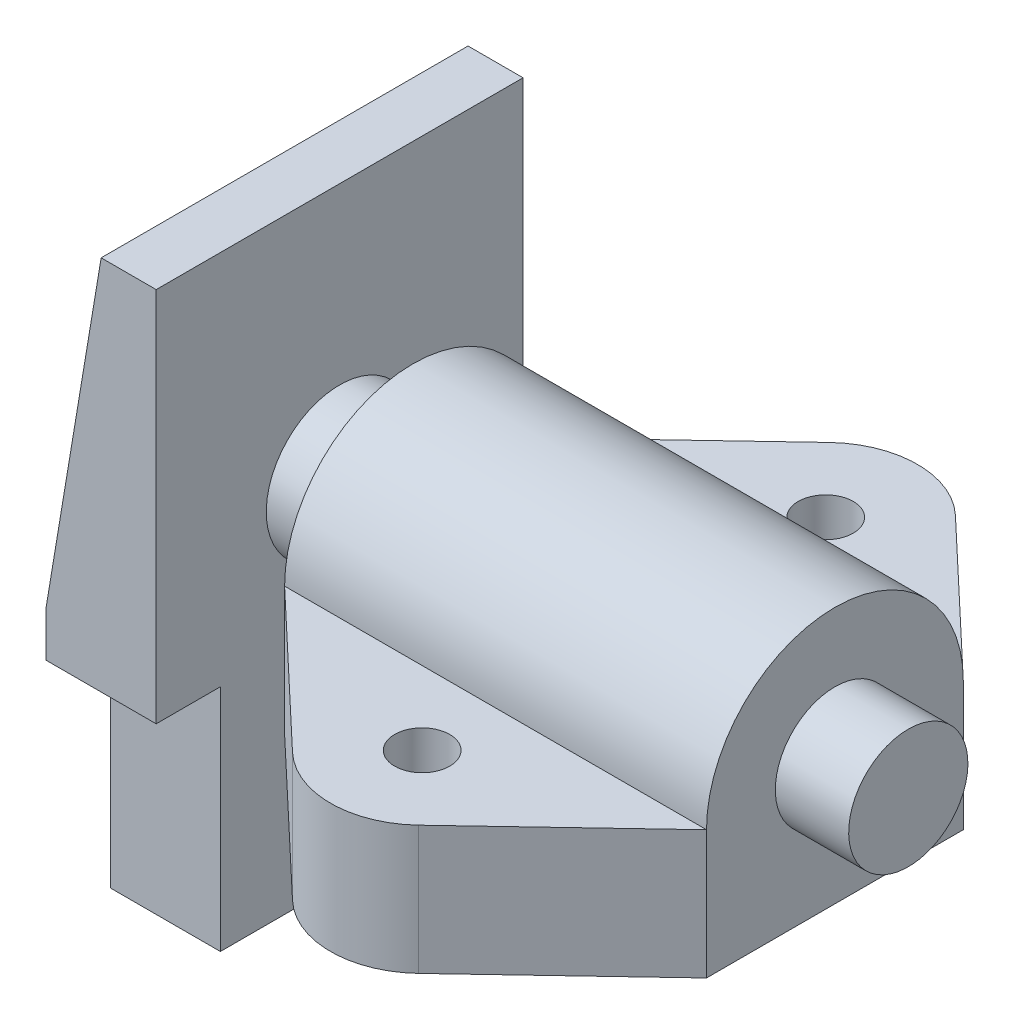
SolidWorks part; units mm, degrees
ref_plane "Piano frontale" through (0, 0, 0) normal (0, 0, 1) x (1, 0, 0)
ref_plane "Piano superiore" through (0, 0, 0) normal (0, 1, 0) x (1, 0, 0)
ref_plane "Piano destro" through (0, 0, 0) normal (1, 0, 0) x (0, 0, -1)
sketch "Schizzo1" plane through (0, 0, 0) normal (0, 0, 1) x (1, 0, 0)
  line L0 (0, 33) -> (6, 33)
  line L1 (6, 33) -> (6, -33)
  line L2 (0, 33) -> (-6, -3)
  line L3 (-6, -3) -> (-6, -33)
  line L4 (-6, -33) -> (6, -33)
  line L5 (55, 0) -> (-55, 0) construction
  line L6 (0, -55) -> (0, 55) construction
  dimension "D1" = 36
  dimension "D2" = 66
  dimension "D3" = 33
  dimension "D4" = 12
  dimension "D5" = 6
  dimension "D6" = 6
extrude "Estrusione-Estrusione1" add sketch "Schizzo1" along normal mid plane 40
sketch "Schizzo2" plane through (0, 0, 20) normal (0, 0, 1) x (1, 0, 0)
  line L0 (-6, -8) -> (6, -8)
  line L1 (-6, -3) -> (-6, -33) construction
  line L2 (6, -33) -> (6, 33) construction
  line L3 (6, -8) -> (6, -33)
  line L4 (6, -33) -> (-6, -33)
  line L5 (-6, -33) -> (6, -33) construction
  line L6 (-6, -33) -> (-6, -8)
  dimension "D1" = 5
extrude "Taglio-Estrusione1" cut sketch "Schizzo2" against normal blind 7
mirror "Specchia1" about plane through (0, 0, 0) normal (0, 0, 1) of "Taglio-Estrusione1"
sketch "Schizzo3" plane through (6, 0, 0) normal (1, 0, 0) x (0, 0, -1)
  line L0 (0, 6.6) -> (0, -6.6) construction
  line L1 (-13, -8) -> (-20, -8) construction
  circle A0 centre (0, 6) radius 8
  dimension "D1" = 16
  dimension "D2" = 14
extrude "Estrusione-Estrusione2" add sketch "Schizzo3" along normal blind 8
sketch "Schizzo4" plane through (14, 0, 0) normal (1, 0, 0) x (0, 0, -1)
  line L0 (-14, 6) -> (-14, -8)
  line L1 (-14, -8) -> (14, -8)
  line L2 (14, -8) -> (14, 6)
  arc A0 (14, 6) -> (-14, 6) centre (0, 6) ccw
  dimension "D1" = 28
extrude "Estrusione-Estrusione3" add sketch "Schizzo4" along normal blind 46
ref_plane "Piano1" through (0, 6, 0) normal (0, 1, 0) x (1, 0, 0)
sketch "Schizzo5" plane through (0, 6, 0) normal (0, 1, 0) x (1, 0, 0)
  line L0 (14, -14) -> (60, -14)
  line L1 (14, -14) -> (30.126, -29.2628)
  line L2 (60, -14) -> (43.874, -29.2628)
  arc A0 (30.126, -29.2628) -> (43.874, -29.2628) centre (37, -22) ccw
  point P5 (30.126, -29.2628)
  point P6 (37, -14)
  dimension "D1" = 20
  dimension "D2" = 8
extrude "Estrusione-Estrusione5" add sketch "Schizzo5" against normal blind 14
mirror "Specchia2" about plane through (0, 0, 0) normal (0, 0, 1) of "Estrusione-Estrusione5"
sketch "Schizzo6" plane through (60, 0, 0) normal (1, 0, 0) x (0, 0, -1)
  circle A0 centre (0, 6) radius 6.5
  arc A1 (14, 6) -> (-14, 6) centre (0, 6) ccw construction
  point P3 (0, 0)
  dimension "D1" = 13
extrude "Estrusione-Estrusione6" add sketch "Schizzo6" along normal blind 8
sketch "Schizzo7" plane through (0, 6, 0) normal (0, 1, 0) x (1, 0, 0)
  circle A0 centre (37, -22) radius 3
  arc A1 (30.126, -29.2628) -> (43.874, -29.2628) centre (37, -22) ccw construction
  dimension "D1" = 6
extrude "Taglio-Estrusione2" cut sketch "Schizzo7" against normal through all
mirror "Specchia3" about plane through (0, 0, 0) normal (0, 0, 1) of "Taglio-Estrusione2"
